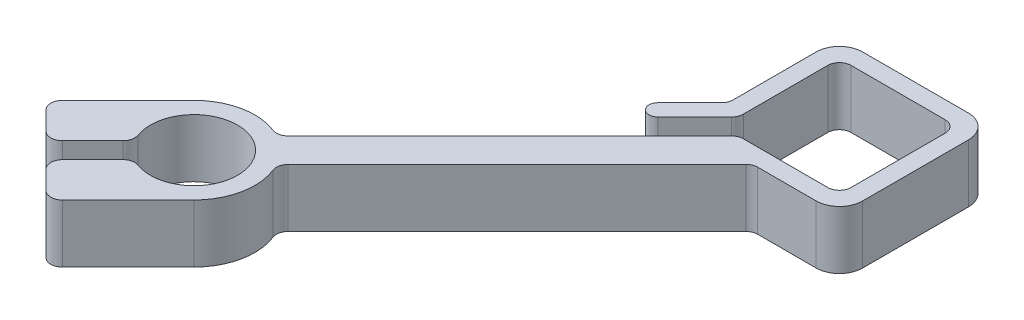
SolidWorks part; units mm, degrees
ref_plane "Спереди" through (0, 0, 0) normal (0, 0, 1) x (1, 0, 0)
ref_plane "Сверху" through (0, 0, 0) normal (0, 1, 0) x (1, 0, 0)
ref_plane "Справа" through (0, 0, 0) normal (1, 0, 0) x (0, 0, -1)
sketch "Эскиз1" plane through (0, 0, 0) normal (0, 1, 0) x (1, 0, 0)
  line L0 (-13.1, 13.1) -> (-13.1, -6.0289)
  line L1 (-10.1, 10.1) -> (10.1, 10.1)
  line L2 (-10.1, 10.1) -> (-10.1, -7.2716)
  line L3 (-10.1, -10.1) -> (-7.2716, -10.1) construction
  line L4 (10.1, 10.1) -> (10.1, -10.1)
  line L5 (-10.1, 10.1) -> (10.1, -10.1) construction
  line L6 (-10.1, -10.1) -> (10.1, 10.1) construction
  line L7 (-13.1, -13.1) -> (-10.2716, -13.1) construction
  line L8 (13.1, 13.1) -> (13.1, -13.1)
  line L9 (-13.1, 13.1) -> (13.1, 13.1)
  line L10 (-7.2716, -10.1) -> (-46.9971, -49.8255)
  line L11 (-10.1, -7.2716) -> (-17.0393, -14.2109)
  line L12 (-10.2716, -13.1) -> (-1.7863, -13.1) construction
  line L13 (-13.1, -13.1) -> (13.1, -13.1) construction
  line L14 (-13.1, -10.2716) -> (-13.1, -13.1) construction
  line L15 (-13.1, 13.1) -> (-13.1, -13.1) construction
  line L16 (-10.1, -7.2716) -> (-10.1, -10.1) construction
  line L17 (-10.1, 10.1) -> (-10.1, -10.1) construction
  line L18 (-7.2716, -10.1) -> (10.1, -10.1)
  line L19 (-10.1, -10.1) -> (10.1, -10.1) construction
  line L20 (-13.1, -6.0289) -> (-19.1607, -12.0896)
  line L21 (-1.7863, -13.1) -> (-42.7544, -54.0681)
  line L22 (-1.7863, -13.1) -> (13.1, -13.1)
  line L23 (-13.1, -6.0289) -> (-13.1, -10.2716) construction
  line L25 (-6.0289, -13.1) -> (-67.7675, -74.8386) construction
  line L26 (-59.4155, -51.6373) -> (-72.1434, -64.3652)
  line L27 (-72.1434, -64.3652) -> (-66.133, -70.3756)
  line L28 (-57.2942, -79.2145) -> (-44.5663, -66.4866)
  line L29 (-58.5163, -62.759) -> (-66.133, -70.3756)
  line L30 (-63.3046, -73.2041) -> (-55.6879, -65.5874)
  line L31 (-63.3046, -73.2041) -> (-57.2942, -79.2145)
  arc A0 (-55.6879, -65.5874) -> (-58.5163, -62.759) centre (-51.9909, -59.0619) ccw
  arc A1 (-46.9971, -49.8255) -> (-59.4155, -51.6373) centre (-51.9909, -59.0619) ccw
  arc A2 (-60.6938, -64.9364) -> (-57.8653, -67.7648) centre (-51.9909, -59.0619) ccw construction
  circle A3 centre (-51.9909, -59.0619) radius 10.5 construction
  arc A4 (-44.5663, -66.4866) -> (-42.7544, -54.0681) centre (-51.9909, -59.0619) ccw
  arc A5 (-19.1607, -12.0896) -> (-17.0393, -14.2109) centre (-18.1, -13.1503) ccw
  circle A6 centre (-51.9909, -59.0619) radius 7.5 construction
  point P20 (0, 0)
  point P26 (-41.9497, -55.992)
  point P35 (-44.8186, -56.8692)
  dimension "D9" = 15
  dimension "D1" = 20.2
  dimension "D2" = 20.2
  dimension "D4" = 2
  dimension "D5" = 2
  dimension "D6" = 3
  dimension "D7" = 6
  dimension "D8" = 5
  dimension "D11" = 65
  dimension "D12" = 18
  dimension "D13" = 2
  dimension "D14" = 2
  dimension "D3" = 3
  dimension "D10" = 3
extrude "Бобышка-Вытянуть1" add sketch "Эскиз1" along normal blind 10
fillet "Скругление1" radius 2 15 edges at (-55.6879, 5, 65.5874) (-58.5163, 5, 62.759) (-57.2942, 5, 79.2145) (-63.3046, 5, 73.2041) (-66.133, 5, 70.3756) (-72.1434, 5, 64.3652) (-46.9971, 5, 49.8255) (-42.7544, 5, 54.0681) (-1.7863, 5, 13.1) (-13.1, 5, 6.0289) (10.1, 5, 10.1) (-7.2716, 5, 10.1) (-10.1, 5, 7.2716) (-10.1, 5, -10.1) (10.1, 5, -10.1)
fillet "Скругление2" radius 4 3 edges at (13.1, 5, 13.1) (13.1, 5, -13.1) (-13.1, 5, -13.1)
